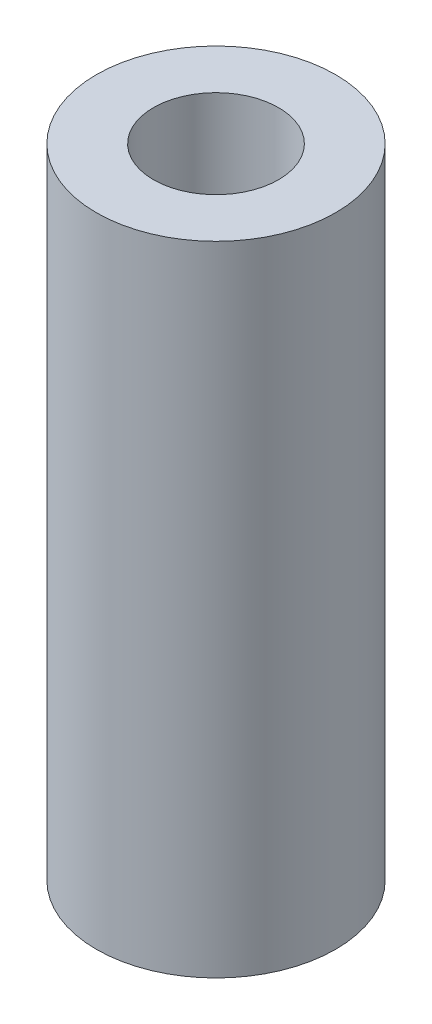
SolidWorks part; units mm, degrees
material "6061-T6 (SS)"
ref_plane "Front Plane" through (0, 0, 0) normal (0, 0, 1) x (1, 0, 0)
ref_plane "Top Plane" through (0, 0, 0) normal (0, 1, 0) x (1, 0, 0)
ref_plane "Right Plane" through (0, 0, 0) normal (1, 0, 0) x (0, 0, -1)
other "Bounding Box"
ref_plane "Default Plane" through (13.8565, 3.175, 6.7999) normal (0, -1, 0) x (-1, 0, 0)
sketch "Sketch1" plane through (0, 0, 0) normal (0, 1, 0) x (1, 0, 0)
  circle A0 centre (0, 0) radius 4.7625
  circle A1 centre (0, 0) radius 2.4892
  dimension "D1" = 9.525
  dimension "D2" = 4.9784
extrude "Boss-Extrude1" add sketch "Sketch1" along normal mid plane 25.4
